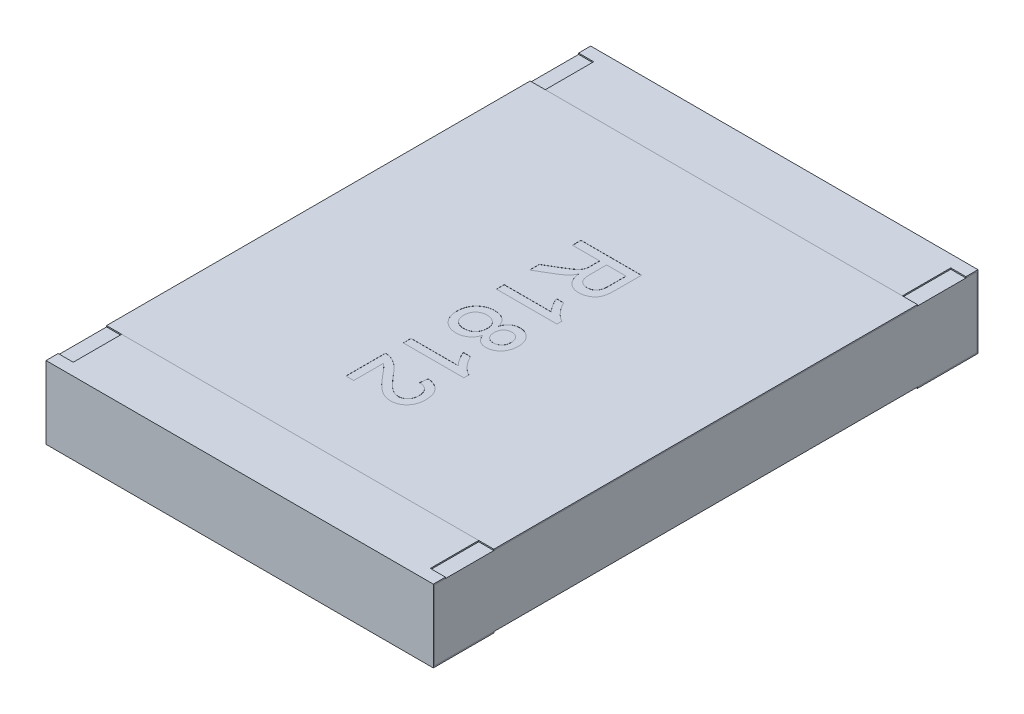
SolidWorks part; units mm, degrees
ref_plane "Front Plane" through (0, 0, 0) normal (0, 0, 1) x (1, 0, 0)
ref_plane "Top Plane" through (0, 0, 0) normal (0, 1, 0) x (1, 0, 0)
ref_plane "Right Plane" through (0, 0, 0) normal (1, 0, 0) x (0, 0, -1)
sketch "Sketch4" plane through (0, 0, 0) normal (1, 0, 0) x (0, 0, -1)
  line L0 (0, 0.1169) -> (0, -0.0721) construction
  line L1 (-2.25, 0) -> (0.3788, 0) construction
  line L2 (-2.25, 0.3) -> (-2.25, -0.3)
  line L3 (-2.25, -0.3) -> (-1.75, -0.3)
  line L4 (-1.75, 0.3) -> (-1.75, 0.29)
  line L5 (-1.75, 0.29) -> (-2.24, 0.29)
  line L6 (-2.24, 0.29) -> (-2.24, -0.29)
  line L7 (-2.24, -0.29) -> (-1.75, -0.29)
  line L8 (-1.75, -0.29) -> (-1.75, -0.3)
  line L9 (-1.75, 0.3) -> (-2.25, 0.3)
  line L10 (1.75, 0.3) -> (2.25, 0.3)
  line L11 (1.75, -0.29) -> (1.75, -0.3)
  line L12 (2.24, -0.29) -> (1.75, -0.29)
  line L13 (2.24, 0.29) -> (2.24, -0.29)
  line L14 (1.75, 0.29) -> (2.24, 0.29)
  line L15 (1.75, 0.3) -> (1.75, 0.29)
  line L16 (2.25, -0.3) -> (1.75, -0.3)
  line L17 (2.25, 0.3) -> (2.25, -0.3)
  dimension "LENGTH" = 2.25
  dimension "HEIGHT" = 0.6
  dimension "END CAP TOP LENGTH" = 0.5
  dimension "END CAP BOTTOM LENGTH" = 0.5
  dimension "D5" = 0.01
  dimension "D6" = 0.01
extrude "Boss-Extrude2" add sketch "Sketch4" along normal mid plane 3.2
sketch "Sketch5" plane through (0, 0, 0) normal (1, 0, 0) x (0, 0, -1)
  line L1 (-2.24, 0.29) -> (2.24, 0.29)
  line L2 (-2.24, 0.29) -> (-2.24, -0.29)
  line L3 (-2.24, -0.29) -> (2.24, -0.29)
  line L4 (2.24, 0.29) -> (2.24, -0.29)
extrude "Boss-Extrude3" add sketch "Sketch5" along normal up to surface and the other way up to surface separate body
sketch "Sketch6" plane through (0, 0.3, 0) normal (0, 1, 0) x (1, 0, 0)
  line L0 (-1.6, 2.25) -> (-1.6, 1.75) construction
  line L1 (-1.6, 2.15) -> (-1.475, 2.15)
  line L2 (-1.6, 2.15) -> (-1.6, 1.75)
  line L3 (-1.6, 1.75) -> (-1.475, 1.75)
  line L4 (-1.475, 2.15) -> (-1.475, 1.75)
  line L5 (1.6, 1.75) -> (-1.6, 1.75) construction
  line L6 (0, 0.0345) -> (0, -0.0345) construction
  line L7 (-0.0325, 0) -> (0.03, 0) construction
  line L8 (1.6, 2.15) -> (1.6, 1.75)
  line L9 (1.6, 1.75) -> (1.475, 1.75)
  line L10 (1.475, 2.15) -> (1.475, 1.75)
  line L11 (1.6, 2.15) -> (1.475, 2.15)
  line L12 (1.6, -2.15) -> (1.475, -2.15)
  line L13 (1.6, -2.15) -> (1.6, -1.75)
  line L14 (1.6, -1.75) -> (1.475, -1.75)
  line L15 (1.475, -2.15) -> (1.475, -1.75)
  line L16 (-1.6, -2.15) -> (-1.475, -2.15)
  line L17 (-1.6, -2.15) -> (-1.6, -1.75)
  line L18 (-1.6, -1.75) -> (-1.475, -1.75)
  line L19 (-1.475, -2.15) -> (-1.475, -1.75)
  dimension "TOP CUT WIDTH" = 0.125
  dimension "TOP CUT LENGTH" = 0.4
extrude "Cut-Extrude1" cut sketch "Sketch6" against normal up to surface (0.01 mm away) up to face at (0, 0.29, 0)
sketch "Sketch7" plane through (0, 0.29, 0) normal (0, 1, 0) x (1, 0, 0)
  line L1 (-1.6, 1.75) -> (1.6, 1.75)
  line L2 (-1.6, 1.75) -> (-1.6, -1.75)
  line L3 (-1.6, -1.75) -> (1.6, -1.75)
  line L4 (1.6, 1.75) -> (1.6, -1.75)
  line L5 (1.475, -1.75) -> (-1.475, -1.75) construction
  line L6 (1.475, 1.75) -> (-1.475, 1.75) construction
  line L7 (-1.6, -2.24) -> (-1.6, 2.24) construction
  line L8 (1.6, 2.24) -> (1.6, -2.24) construction
extrude "Boss-Extrude4" add sketch "Sketch7" along normal up to surface (0.01 mm away) separate body up to face at (0, 0.3, -2.075)
sketch "Sketch14" plane through (0, 0.3, 0) normal (0, 1, 0) x (1, 0, 0)
  line L0 (-0.25, 0.8778) -> (-0.25, -0.8778) construction
  line L1 (0, 0) -> (-0.25, 0) construction
  text T0 "R1812" font "Arial" height 0.5
  dimension "D1" = 0.25
extrude "TEXT1812" cut sketch "Sketch14" against normal blind 0.001
